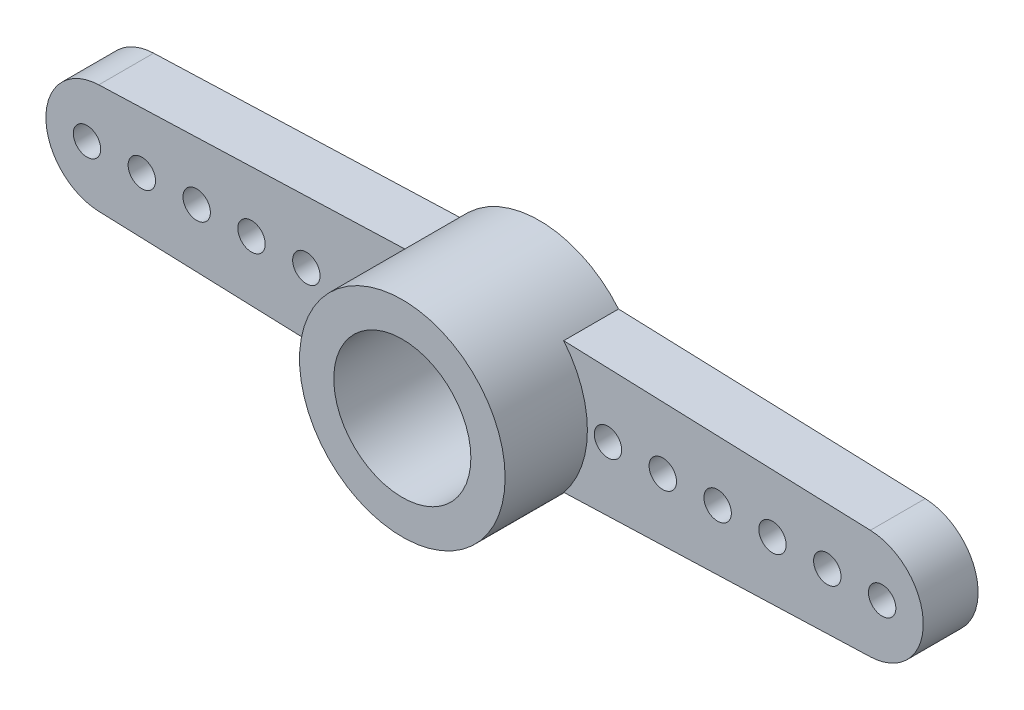
SolidWorks part; units mm, degrees
ref_plane "Спереди" through (0, 0, 0) normal (0, 0, 1) x (1, 0, 0)
ref_plane "Сверху" through (0, 0, 0) normal (0, 1, 0) x (1, 0, 0)
ref_plane "Справа" through (0, 0, 0) normal (1, 0, 0) x (0, 0, -1)
sketch "Эскиз1" plane through (0, 0, 0) normal (0, 0, 1) x (1, 0, 0)
  line L0 (0, 0) -> (-14, 0)
  line L1 (-14.0708, 1.9987) -> (0, 2.4974)
  line L2 (-14.0708, -1.9987) -> (0, -2.4974)
  line L4 (14.0708, -1.9987) -> (0, -2.4974)
  line L5 (14.0708, 1.9987) -> (0, 2.4974)
  circle A0 centre (0, 0) radius 3.75
  circle A1 centre (0, 0) radius 2.5
  arc A2 (-13.967, -1.9997) -> (-14.0708, 1.9987) centre (-14, 0) cw
  arc A3 (13.967, -1.9997) -> (14.0708, 1.9987) centre (14, 0) ccw
  dimension "D1" = 7.5
  dimension "D2" = 5
  dimension "D4" = 2
  dimension "D3" = 14
extrude "Бобышка-Вытянуть3" add sketch "Эскиз1" along normal blind 2
sketch "Эскиз2" plane through (0, 0, 2) normal (0, 0, 1) x (1, 0, 0)
  circle A0 centre (0, 0) radius 3.75
  circle A1 centre (0, 0) radius 2.5
  dimension "D1" = 5
extrude "Бобышка-Вытянуть5" add sketch "Эскиз2" along normal blind 3 separate body
sketch "Эскиз3" plane through (0, 0, 2) normal (0, 0, -1) x (-1, 0, 0)
  circle A0 centre (0, 0) radius 3.75
  circle A1 centre (0, 0) radius 2.5
extrude "Бобышка-Вытянуть6" add sketch "Эскиз3" along normal blind 2
sketch "Эскиз4" plane through (0, 0, 0) normal (0, 0, -1) x (-1, 0, 0)
  line L0 (-16, 0) -> (-14.5, 0)
  line L1 (-14.5, 0) -> (-12.5, 0)
  line L2 (-12.5, 0) -> (-10.5, 0)
  line L3 (-10.5, 0) -> (-8.5, 0)
  line L4 (-8.5, 0) -> (-6.5, 0)
  line L5 (-6.5, 0) -> (-4.5, 0)
  arc A0 (-14.0708, 1.9987) -> (-14.0708, -1.9987) centre (-14, 0) ccw construction
  circle A1 centre (-14.5, 0) radius 0.5
  circle A2 centre (-12.5, 0) radius 0.5
  circle A3 centre (-10.5, 0) radius 0.5
  circle A4 centre (-8.5, 0) radius 0.5
  circle A5 centre (-6.5, 0) radius 0.5
  circle A6 centre (-4.5, 0) radius 0.5
  circle A7 centre (4.5, 0) radius 0.5
  circle A8 centre (6.5, 0) radius 0.5
  circle A9 centre (8.5, 0) radius 0.5
  circle A10 centre (10.5, 0) radius 0.5
  circle A11 centre (12.5, 0) radius 0.5
  circle A12 centre (14.5, 0) radius 0.5
  dimension "D2" = 1
  dimension "D8" = 1
  dimension "D9" = 1
  dimension "D10" = 1
  dimension "D11" = 1
  dimension "D12" = 1
  dimension "D1" = 1.5
  dimension "D3" = 2
  dimension "D4" = 2
  dimension "D5" = 2
  dimension "D6" = 2
  dimension "D7" = 2
extrude "Вырез-Вытянуть1" cut sketch "Эскиз4" against normal blind 2
sketch "Эскиз5" plane through (0, 0, 0) normal (0, 0, -1) x (-1, 0, 0)
  circle A0 centre (0, 0) radius 2.5
extrude "Бобышка-Вытянуть7" add sketch "Эскиз5" against normal blind 1
sketch "Эскиз6" plane through (0, 0, 0) normal (0, 0, -1) x (-1, 0, 0)
  circle A0 centre (0, 0) radius 2.5
  dimension "D1" = 5
extrude "Вырез-Вытянуть2" cut sketch "Эскиз6" against normal blind 0.5
sketch "Эскиз7" plane through (0, 0, 0.5) normal (0, 0, -1) x (-1, 0, 0)
  circle A0 centre (0, 0) radius 1.25
  dimension "D1" = 2.5
extrude "Вырез-Вытянуть3" cut sketch "Эскиз7" against normal blind 5
sketch "Эскиз8" plane through (0, 0, 0.5) normal (0, 0, -1) x (-1, 0, 0)
  line L0 (-2.8252, -0.1999) -> (-2.8894, -0.2509)
